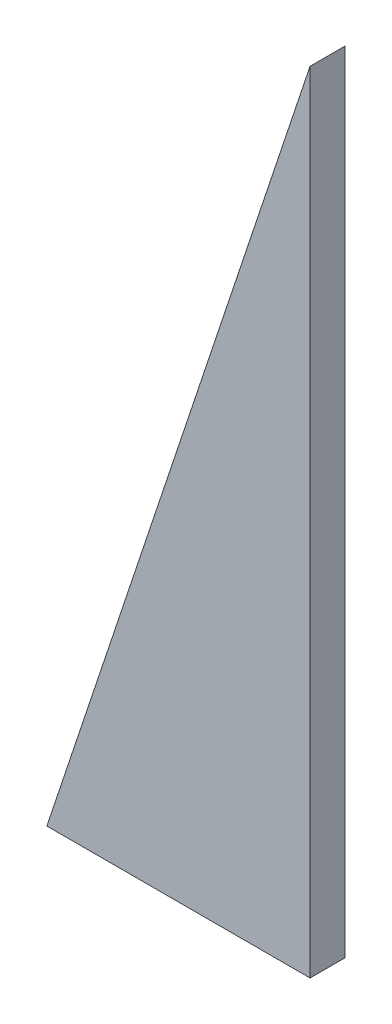
SolidWorks part; units mm, degrees
material "AISI 1045 Steel, cold drawn"
ref_plane "Front Plane" through (0, 0, 0) normal (0, 0, 1) x (1, 0, 0)
ref_plane "Top Plane" through (0, 0, 0) normal (0, 1, 0) x (1, 0, 0)
ref_plane "Right Plane" through (0, 0, 0) normal (1, 0, 0) x (0, 0, -1)
sketch "Sketch1" plane through (0, 0, 0) normal (0, 0, 1) x (1, 0, 0)
  line L0 (0, 0) -> (0, 180)
  line L1 (0, 180) -> (-60, 0)
  line L2 (-60, 0) -> (0, 0)
  dimension "D1" = 180
  dimension "D2" = 60
extrude "Boss-Extrude1" add sketch "Sketch1" along normal mid plane 8
